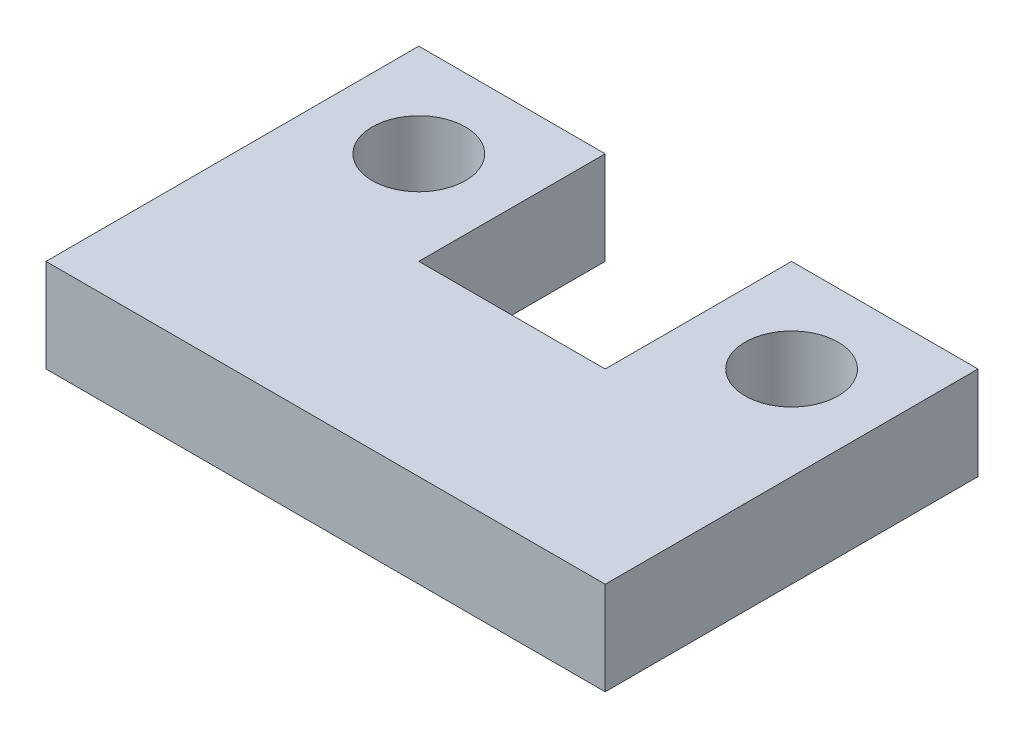
SolidWorks part; units mm, degrees
ref_plane "Front Plane" through (0, 0, 0) normal (0, 0, 1) x (1, 0, 0)
ref_plane "Top Plane" through (0, 0, 0) normal (0, 1, 0) x (1, 0, 0)
ref_plane "Right Plane" through (0, 0, 0) normal (1, 0, 0) x (0, 0, -1)
sketch "Sketch2" plane through (0, 0, 0) normal (0, 1, 0) x (1, 0, 0)
  line L0 (0, 0) -> (120, 0)
  line L1 (120, 0) -> (120, 80)
  line L2 (120, 80) -> (80, 80)
  line L3 (80, 80) -> (80, 40)
  line L4 (80, 40) -> (40, 40)
  line L5 (40, 40) -> (40, 80)
  line L6 (40, 80) -> (0, 80)
  line L7 (0, 80) -> (0, 0)
  dimension "D1" = 80
  dimension "D2" = 80
  dimension "D3" = 40
  dimension "D4" = 40
  dimension "D5" = 120
  dimension "D6" = 40
extrude "Boss-Extrude1" add sketch "Sketch2" along normal blind 20
sketch "Sketch4" plane through (0, 0, 0) normal (0, -1, 0) x (1, 0, 0)
  line L0 (0, -80) -> (0, 0) construction
  line L1 (40, -80) -> (0, -80) construction
  line L2 (80, -80) -> (80, -40) construction
  line L3 (120, -80) -> (80, -80) construction
  circle A0 centre (20, -60) radius 10
  circle A1 centre (100, -60) radius 10
  dimension "D1" = 20
  dimension "D2" = 20
  dimension "D3" = 20
  dimension "D4" = 20
  dimension "D5" = 20
  dimension "D6" = 20
extrude "Cut-Extrude1" cut sketch "Sketch4" against normal blind 20
